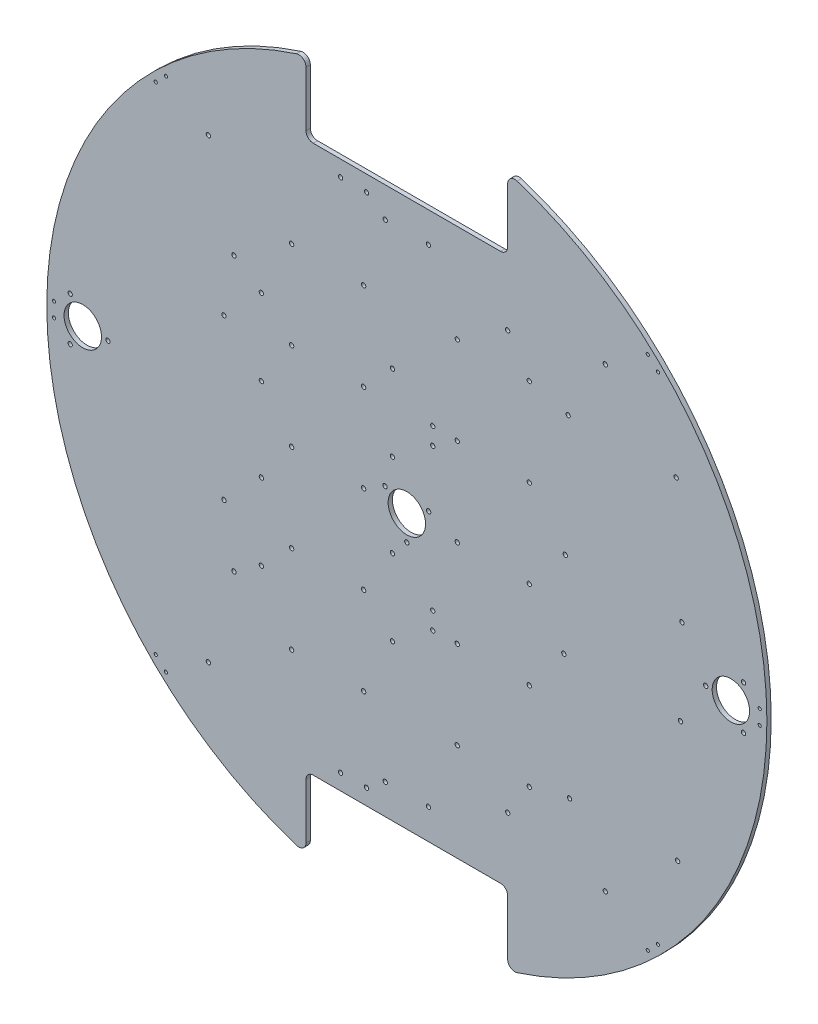
SolidWorks part; units mm, degrees
material "ｱｸﾘﾙ (中-上級の耐衝撃性)"
ref_plane "正面" through (0, 0, 0) normal (0, 0, 1) x (1, 0, 0)
ref_plane "平面" through (0, 0, 0) normal (0, 1, 0) x (1, 0, 0)
ref_plane "右側面" through (0, 0, 0) normal (1, 0, 0) x (0, 0, -1)
sketch "ｽｹｯﾁ1" plane through (0, 0, 0) normal (0, 0, 1) x (1, 0, 0)
  line L0 (0, -250) -> (0, 250) construction
  line L1 (-250, 0) -> (250, 0) construction
  circle A0 centre (0, 0) radius 250
  dimension "D1" = 500
extrude "ﾎﾞｽ - 押し出し1" add sketch "ｽｹｯﾁ1" against normal blind 3
sketch "ｽｹｯﾁ2" plane through (0, 0, 0) normal (0, 0, 1) x (1, 0, 0)
  line L0 (0, 250) -> (0, -250) construction
  line L1 (-250, 0) -> (250, 0) construction
  line L2 (0, 190) -> (52.533, 190) construction
  line L3 (0, 190) -> (-70, 190) construction
  line L5 (0, 190) -> (70, 190)
  line L7 (0, 250) -> (70, 250)
  line L8 (70, 190) -> (70, 250)
  line L9 (0, 190) -> (-70, 190)
  line L11 (0, 250) -> (-70, 250)
  line L12 (-70, 190) -> (-70, 250)
  circle A0 centre (0, 0) radius 250 construction
extrude "ｶｯﾄ - 押し出し1" cut sketch "ｽｹｯﾁ2" against normal through all
sketch "ｽｹｯﾁ3" plane through (0, 0, 0) normal (0, 0, 1) x (1, 0, 0)
  line L0 (0, 190) -> (0, -250) construction
  line L1 (-70, 190) -> (70, 190) construction
  line L2 (-250, 0) -> (250, 0) construction
  line L3 (-61.1353, -190) -> (70, -190) construction
  line L5 (0, -250) -> (70, -250)
  line L7 (0, -190) -> (70, -190)
  line L8 (70, -250) -> (70, -190)
  line L9 (0, -250) -> (-70, -250)
  line L11 (0, -190) -> (-70, -190)
  line L12 (-70, -250) -> (-70, -190)
  arc A0 (-70, 240) -> (70, 240) centre (0, 0) ccw construction
  dimension "D1" = 190
  dimension "D2" = 140
  dimension "D4" = 60
extrude "ｶｯﾄ - 押し出し2" cut sketch "ｽｹｯﾁ3" against normal through all
fillet "ﾌｨﾚｯﾄ1" radius 5 1 edges at (-70, 240, -1.5)
fillet "ﾌｨﾚｯﾄ2" radius 5 1 edges at (70, 240, -1.5)
fillet "ﾌｨﾚｯﾄ3" radius 5 1 edges at (70, 190, -1.5)
fillet "ﾌｨﾚｯﾄ4" radius 5 1 edges at (-70, 190, -1.5)
fillet "ﾌｨﾚｯﾄ5" radius 5 1 edges at (-70, -240, -1.5)
fillet "ﾌｨﾚｯﾄ6" radius 5 1 edges at (70, -190, -1.5)
fillet "ﾌｨﾚｯﾄ7" radius 5 1 edges at (70, -240, -1.5)
fillet "ﾌｨﾚｯﾄ8" radius 5 1 edges at (-70, -190, -1.5)
sketch "ｽｹｯﾁ4" plane through (0, 0, 0) normal (0, 0, 1) x (1, 0, 0)
  line L0 (0, 190) -> (0, -190) construction
  line L1 (-65, 190) -> (65, 190) construction
  line L2 (65, -190) -> (-65, -190) construction
  line L3 (-65, 190) -> (65, 190) construction
  line L4 (0, 179) -> (-56, 179) construction
  line L5 (0, -179) -> (-49.4125, -179) construction
  circle A0 centre (15, 169) radius 1.5
  circle A1 centre (-15, 169) radius 1.5
  circle A2 centre (15, -169) radius 1.5
  circle A3 centre (-15, -169) radius 1.5
  circle A4 centre (-46, 179) radius 1.5
  circle A5 centre (-28, 179) radius 1.5
  circle A6 centre (-46, -179) radius 1.5
  circle A7 centre (-28, -179) radius 1.5
  dimension "D2" = 30
  dimension "D3" = 21
  dimension "D5" = 28
  dimension "D6" = 11
  dimension "D11" = 21
  dimension "D12" = 21
  dimension "D13" = 28
  dimension "D14" = 18
  dimension "D4" = 30
  dimension "D7" = 18
  dimension "D15" = 11
extrude "ｶｯﾄ - 押し出し3" cut sketch "ｽｹｯﾁ4" against normal through all
sketch "ｽｹｯﾁ15" plane through (0, 0, 0) normal (0, 0, 1) x (1, 0, 0)
  line L0 (0, 0) -> (164.0477, 188.6488) construction
  line L1 (-250, 0) -> (250, 0) construction
  line L2 (0, 190) -> (0, -190) construction
  line L3 (0, 0) -> (164.0477, -188.6488) construction
  line L4 (0, 0) -> (-164.0477, -188.6488) construction
  line L5 (0, 0) -> (-164.0477, 188.6488) construction
  line L6 (-65, 190) -> (65, 190) construction
  line L7 (65, -190) -> (-65, -190) construction
  arc A0 (76.5306, -237.998) -> (76.5306, 237.998) centre (0, 0) ccw construction
  arc A1 (-76.5306, 237.998) -> (-76.5306, -237.998) centre (0, 0) ccw construction
  circle A2 centre (137.8001, 158.465) radius 1.5
  circle A3 centre (137.8001, -158.465) radius 1.5
  circle A4 centre (-137.8001, -158.465) radius 1.5
  circle A5 centre (-137.8001, 158.465) radius 1.5
  point P0 (0, 0)
  dimension "D5" = 210
  dimension "D6" = 210
  dimension "D7" = 48.99
  dimension "D8" = 210
  dimension "D9" = 210
  dimension "D1" = 3
  dimension "D2" = 48.99
  dimension "D3" = 48.99
  dimension "D4" = 48.99
extrude "ｶｯﾄ - 押し出し5" cut sketch "ｽｹｯﾁ15" against normal through all
sketch "ｽｹｯﾁ17" plane through (0, 0, 0) normal (0, 0, 1) x (1, 0, 0)
  line L0 (0, 190) -> (0, -190) construction
  line L1 (-65, 190) -> (65, 190) construction
  line L2 (65, -190) -> (-65, -190) construction
  line L3 (-250, 0) -> (250, 0) construction
  arc A0 (-76.5306, 237.998) -> (-76.5306, -237.998) centre (0, 0) ccw construction
  arc A1 (76.5306, -237.998) -> (76.5306, 237.998) centre (0, 0) ccw construction
  circle A2 centre (-30, 122) radius 1.5
  circle A3 centre (35, 122) radius 1.5
  circle A4 centre (35, -122) radius 1.5
  circle A5 centre (-30, -122) radius 1.5
  circle A6 centre (35, 61) radius 1.5
  circle A7 centre (35, -61) radius 1.5
  circle A8 centre (-80, 122) radius 1.5
  circle A9 centre (-80, -122) radius 1.5
  circle A10 centre (85, -122) radius 1.5
  circle A11 centre (85, 122) radius 1.5
  circle A12 centre (-30, -61) radius 1.5
  circle A13 centre (-30, 61) radius 1.5
  circle A14 centre (-80, 61) radius 1.5
  circle A15 centre (-80, -61) radius 1.5
  circle A16 centre (85, -61) radius 1.5
  circle A17 centre (85, 61) radius 1.5
  circle A18 centre (-80, 0) radius 1.5
  circle A19 centre (-30, 0) radius 1.5
  circle A20 centre (35, 0) radius 1.5
  circle A21 centre (85, 0) radius 1.5
  dimension "D3" = 61
  dimension "D4" = 122
  dimension "D6" = 50
  dimension "D7" = 244
  dimension "D24" = 30
  dimension "D25" = 35
  dimension "D1" = 122
extrude "ｶｯﾄ - 押し出し7" cut sketch "ｽｹｯﾁ17" against normal through all
sketch "ｽｹｯﾁ18" plane through (0, 0, 0) normal (0, 0, 1) x (1, 0, 0)
  line L4 (-250, 0) -> (250, 0) construction
  line L5 (225, 0) -> (239.6031, 25.2934) construction
  line L6 (225, 0) -> (238.6261, -23.6011) construction
  line L7 (-225, 0) -> (-237.9087, 22.3585) construction
  line L8 (-225, 0) -> (-244.3592, -33.5311) construction
  line L9 (0, 0) -> (0, -29.9839) construction
  line L10 (0, 0) -> (28.8216, 16.6402) construction
  line L11 (0, 0) -> (-30.2415, 17.4599) construction
  circle A0 centre (0, 0) radius 13
  circle A1 centre (225, 0) radius 13
  circle A2 centre (-225, 0) radius 13
  arc A3 (76.5306, -237.998) -> (76.5306, 237.998) centre (0, 0) ccw construction
  arc A4 (-76.5306, 237.998) -> (-76.5306, -237.998) centre (0, 0) ccw construction
  circle A5 centre (-15.1554, 8.75) radius 1.5
  circle A6 centre (15.1554, 8.75) radius 1.5
  circle A7 centre (0, -17.5) radius 1.5
  circle A8 centre (-233.75, 15.1554) radius 1.5
  circle A9 centre (-233.75, -15.1554) radius 1.5
  circle A10 centre (-207.5, 0) radius 1.5
  circle A11 centre (233.75, 15.1554) radius 1.5
  circle A12 centre (233.75, -15.1554) radius 1.5
  circle A13 centre (207.5, 0) radius 1.5
  dimension "D1" = 26
  dimension "D22" = 17.5
  dimension "D12" = 120
extrude "ｶｯﾄ - 押し出し8" cut sketch "ｽｹｯﾁ18" against normal through all
sketch "ｽｹｯﾁ19" plane through (0, 0, 0) normal (0, 0, 1) x (1, 0, 0)
  line L0 (-250, 0) -> (250, 0) construction
  line L1 (150, 0) -> (150, 125) construction
  line L2 (150, 0) -> (150, -133.5922) construction
  line L3 (0, 190) -> (0, -190) construction
  line L4 (-65, 190) -> (65, 190) construction
  line L5 (65, -190) -> (-65, -190) construction
  arc A0 (-76.5306, 237.998) -> (-76.5306, -237.998) centre (0, 0) ccw construction
  arc A1 (76.5306, -237.998) -> (76.5306, 237.998) centre (0, 0) ccw construction
  circle A2 centre (187, 115) radius 1.5
  circle A3 centre (112, 115) radius 1.5
  circle A4 centre (110, 30) radius 1.5
  circle A5 centre (191, 30) radius 1.5
  circle A6 centre (190, -30) radius 1.5
  circle A7 centre (109, -30) radius 1.5
  circle A8 centre (113, -115) radius 1.5
  circle A9 centre (188, -115) radius 1.5
  dimension "D1" = 38
  dimension "D2" = 37
  dimension "D4" = 30
  dimension "D6" = 41
  dimension "D7" = 40
  dimension "D8" = 41
  dimension "D9" = 40
  dimension "D3" = 30
  dimension "D10" = 37
  dimension "D11" = 38
  dimension "D20" = 85
  dimension "D21" = 85
  dimension "D22" = 30
  dimension "D23" = 30
  dimension "D24" = 85
  dimension "D25" = 85
extrude "ｶｯﾄ - 押し出し9" cut sketch "ｽｹｯﾁ19" against normal through all
sketch "ｽｹｯﾁ21" plane through (0, 0, 0) normal (0, 0, 1) x (1, 0, 0)
  line L0 (0, 190) -> (0, -190) construction
  line L1 (-65, 190) -> (65, 190) construction
  line L2 (65, -190) -> (-65, -190) construction
  line L3 (-250, 0) -> (250, 0) construction
  arc A0 (-76.5306, 237.998) -> (-76.5306, -237.998) centre (0, 0) ccw construction
  arc A1 (76.5306, -237.998) -> (76.5306, 237.998) centre (0, 0) ccw construction
  circle A2 centre (-120, 95) radius 1.5
  circle A3 centre (-120, -95) radius 1.5
  circle A4 centre (70, 145) radius 1.5
  circle A5 centre (70, -145) radius 1.5
  dimension "D1" = 120
  dimension "D2" = 95
  dimension "D3" = 95
  dimension "D4" = 120
  dimension "D5" = 70
  dimension "D6" = 145
  dimension "D7" = 145
  dimension "D8" = 70
extrude "ｶｯﾄ - 押し出し11" cut sketch "ｽｹｯﾁ21" against normal through all
sketch "ｽｹｯﾁ22" plane through (0, 0, 0) normal (0, 0, 1) x (1, 0, 0)
  line L0 (0, 190) -> (0, -190) construction
  line L1 (10, 55.5) -> (36.6304, 55.5) construction
  line L2 (18, 62.6858) -> (18, 37.6858) construction
  line L3 (10, 55.5) -> (-138.9779, 55.5) construction
  line L4 (-65, 190) -> (65, 190) construction
  line L5 (-10, 82) -> (-10, 29) construction
  line L6 (-101, 93.7893) -> (-101, 26.0829) construction
  line L7 (65, -190) -> (-65, -190) construction
  line L8 (-250, 0) -> (111.5101, 0) construction
  line L11 (-149.2134, -55.5) -> (32.4586, -55.5) construction
  line L13 (-10, -55.5) -> (-10, -22.1911) construction
  line L14 (-10, -55.5) -> (-10, -73.74) construction
  line L15 (-101, -22.1911) -> (-101, -101.6031) construction
  line L16 (18, -35) -> (18, -63) construction
  circle A4 centre (18, 61.5) radius 1.5
  circle A5 centre (18, 49.5) radius 1.5
  circle A6 centre (-10, 82) radius 1.5
  circle A7 centre (-10, 29) radius 1.5
  circle A8 centre (-101, 29) radius 1.5
  circle A9 centre (-101, 82) radius 1.5
  circle A10 centre (-127, 55.5) radius 1.5
  circle A15 centre (18, -49.5) radius 1.5
  circle A16 centre (18, -61.5) radius 1.5
  circle A17 centre (-10, -82) radius 1.5
  circle A18 centre (-101, -82) radius 1.5
  circle A19 centre (-101, -29) radius 1.5
  circle A20 centre (-10, -29) radius 1.5
  circle A21 centre (-127, -55.5) radius 1.5
  arc A22 (-76.5306, 237.998) -> (-76.5306, -237.998) centre (0, 0) ccw construction
  dimension "D3" = 12
  dimension "D4" = 53
  dimension "D6" = 91
  dimension "D7" = 55.5
  dimension "D8" = 28
  dimension "D9" = 18
  dimension "D10" = 55.5
  dimension "D26" = 53
  dimension "D20" = 26
  dimension "D5" = 26
  dimension "D16" = 91
  dimension "D17" = 28
extrude "ｶｯﾄ - 押し出し12" cut sketch "ｽｹｯﾁ22" against normal through all
sketch "ｽｹｯﾁ23" plane through (0, 0, 0) normal (0, 0, 1) x (1, 0, 0)
  line L0 (-250, 0) -> (250, 0) construction
  line L1 (0, 0) -> (-174.2913, 179.2277) construction
  line L2 (0, 0) -> (-174.2913, -179.2277) construction
  line L3 (0, 0) -> (174.2913, -179.2277) construction
  line L4 (0, 0) -> (174.2913, 179.2277) construction
  line L5 (-174.2913, 179.2277) -> (-115.8046, 237.7143) construction
  line L6 (-174.2913, 179.2277) -> (-227.2464, 126.2725) construction
  line L7 (-250, 0) -> (-250, 58.9914) construction
  line L8 (-250, 0) -> (-250, -95.2589) construction
  line L9 (-174.2913, -179.2277) -> (-117.4324, -236.0866) construction
  line L10 (-174.2913, -179.2277) -> (-227.2464, -126.2725) construction
  line L11 (174.2913, -179.2277) -> (215.9061, -137.6128) construction
  line L12 (174.2913, -179.2277) -> (137.1501, -216.3688) construction
  line L13 (250, 0) -> (250, -126.2725) construction
  line L14 (250, 0) -> (250, 120.8233) construction
  line L15 (174.2913, 179.2277) -> (229.2821, 124.2368) construction
  line L16 (174.2913, 179.2277) -> (115.8046, 237.7143) construction
  arc A0 (-76.5306, 237.998) -> (-76.5306, -237.998) centre (0, 0) ccw construction
  arc A1 (76.5306, -237.998) -> (76.5306, 237.998) centre (0, 0) ccw construction
  circle A2 centre (167.2692, 179.1786) radius 1.1
  circle A3 centre (174.3403, 172.1076) radius 1.1
  circle A4 centre (245, -5) radius 1.1
  circle A5 centre (245, 5) radius 1.1
  circle A6 centre (174.3403, -172.1076) radius 1.1
  circle A7 centre (167.2692, -179.1786) radius 1.1
  circle A8 centre (-167.2692, -179.1786) radius 1.1
  circle A9 centre (-174.3403, -172.1076) radius 1.1
  circle A10 centre (-245, -5) radius 1.1
  circle A11 centre (-245, 5) radius 1.1
  circle A12 centre (-174.341, 172.1069) radius 1.1
  circle A13 centre (-167.2692, 179.1786) radius 1.1
  dimension "D5" = 2.2
  dimension "D6" = 2.2
  dimension "D7" = 2.2
  dimension "D8" = 2.2
  dimension "D9" = 2.2
  dimension "D10" = 2.2
  dimension "D11" = 5
  dimension "D12" = 2.2
  dimension "D14" = 2.2
  dimension "D15" = 2.2
  dimension "D16" = 5
  dimension "D17" = 5
  dimension "D19" = 45.8
  dimension "D20" = 5
  dimension "D22" = 5
  dimension "D23" = 5
  dimension "D24" = 10
  dimension "D25" = 5
  dimension "D30" = 5
  dimension "D31" = 5
  dimension "D32" = 10
  dimension "D38" = 2.2
  dimension "D39" = 2.2
  dimension "D4" = 10
  dimension "D13" = 2.2
  dimension "D21" = 10
  dimension "D26" = 10
  dimension "D27" = 5
  dimension "D28" = 5
  dimension "D29" = 5
  dimension "D1" = 45.8
  dimension "D2" = 45.8
  dimension "D18" = 45.8
extrude "ｶｯﾄ - 押し出し13" cut sketch "ｽｹｯﾁ23" against normal through all
